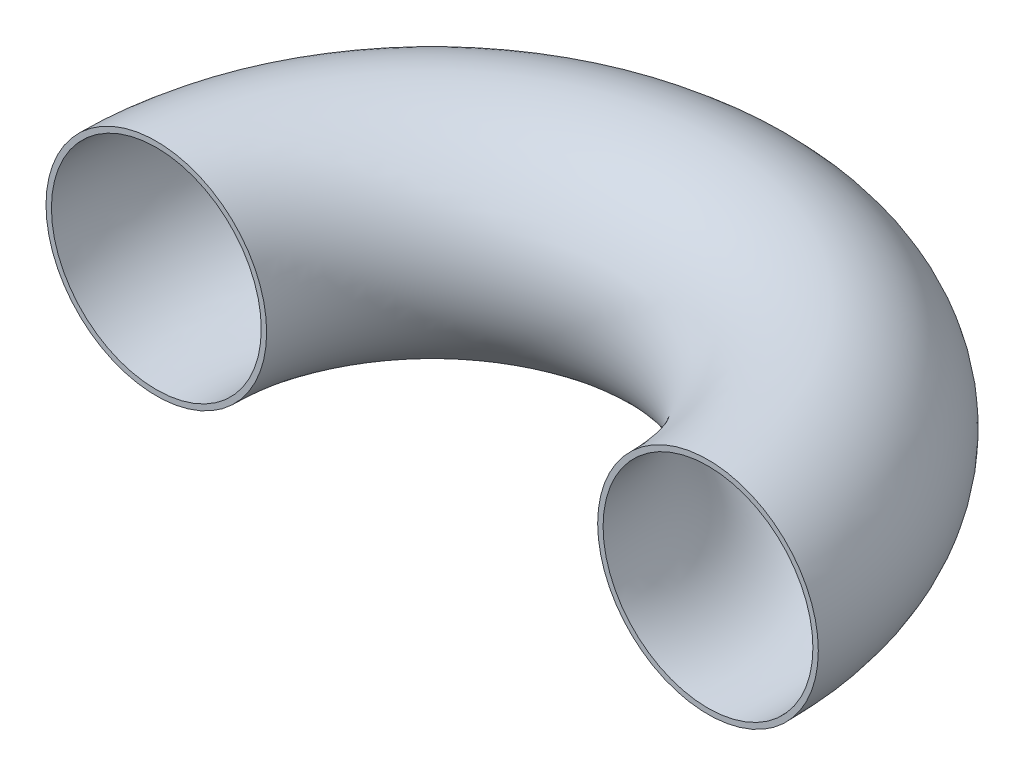
SolidWorks part; units mm, degrees
material "Plain Carbon Steel"
ref_plane "Front Plane" through (0, 0, 0) normal (0, 0, 1) x (1, 0, 0)
ref_plane "Top Plane" through (0, 0, 0) normal (0, 1, 0) x (1, 0, 0)
ref_plane "Right Plane" through (0, 0, 0) normal (1, 0, 0) x (0, 0, -1)
sketch "Sketch2" plane through (0, 0, 0) normal (0, 0, 1) x (1, 0, 0)
  circle A0 centre (0, 0) radius 25.4
  circle A1 centre (0, 0) radius 24.1554
  dimension "D1" = 1.2446
sketch "Sketch3" plane through (0, 0, 0) normal (0, 1, 0) x (1, 0, 0)
  line L0 (0, 0) -> (127, 0) construction
  arc A0 (0, 0) -> (127, 0) centre (63.5, 0) cw
  dimension "D1" = 63.5
sweep "Sweep1" add profiles "Sketch2" path "Sketch3"
